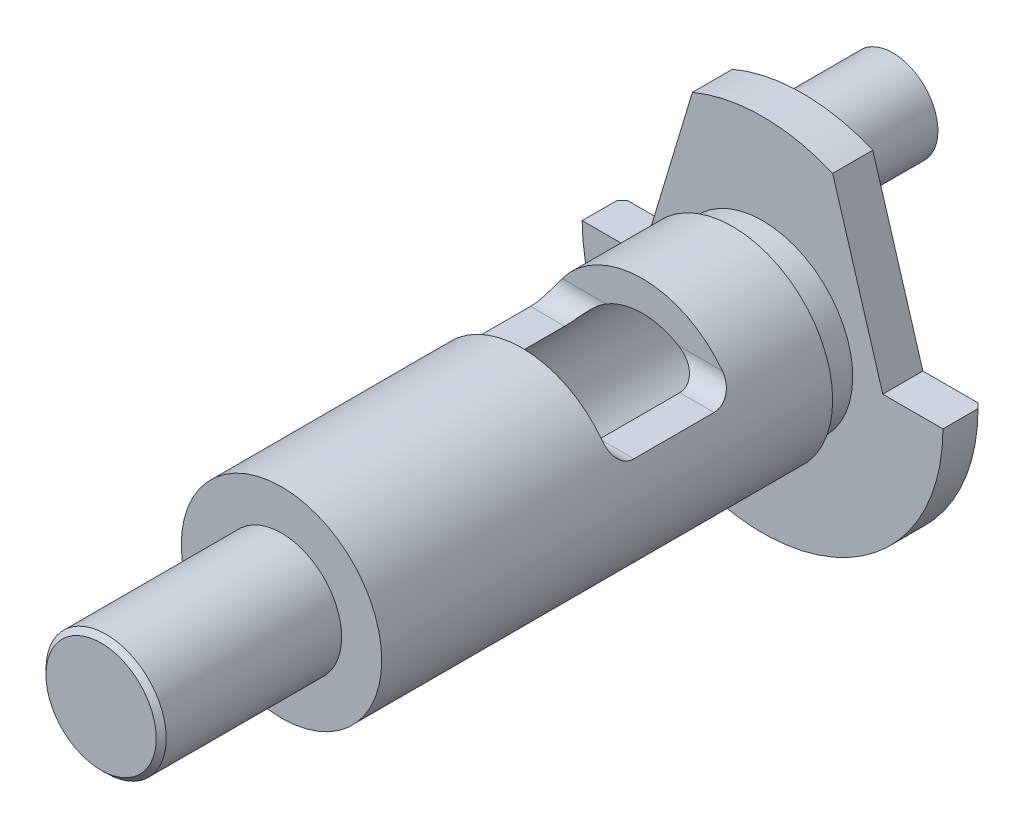
SolidWorks part; units mm, degrees
ref_plane "Plan de face" through (0, 0, 0) normal (0, 0, 1) x (1, 0, 0)
ref_plane "Plan de dessus" through (0, 0, 0) normal (0, 1, 0) x (1, 0, 0)
ref_plane "Plan de droite" through (0, 0, 0) normal (1, 0, 0) x (0, 0, -1)
sketch "Esquisse2" plane through (0, 0, 0) normal (1, 0, 0) x (0, 0, -1)
  line L0 (0, 0) -> (-36, 0) construction
  line L1 (-36, 0) -> (-70, 0)
  line L2 (-70, 0) -> (-70, 6)
  line L3 (-70, 6) -> (-52, 6)
  line L4 (-52, 6) -> (-52, 10)
  line L5 (-52, 10) -> (-7, 10)
  line L6 (-7, 10) -> (-7, 9)
  line L7 (-7, 9) -> (-4, 9)
  line L8 (-4, 9) -> (-4, 18)
  line L9 (-4, 18) -> (0, 18)
  line L10 (0, 18) -> (0, 7)
  line L11 (0, 7) -> (-32, 7)
  line L12 (-32, 7) -> (-36, 0)
  line L13 (0, 7) -> (0, 0) construction
  dimension "D1" = 70
  dimension "D2" = 36
  dimension "D3" = 4
  dimension "D4" = 7
  dimension "D5" = 18
  dimension "D6" = 4
  dimension "D7" = 3
  dimension "D8" = 1
  dimension "D9" = 10
  dimension "D10" = 18
  dimension "D11" = 6
revolve "Révolution2" add sketch "Esquisse2" angle 360 about L0
sketch "Esquisse3" plane through (0, 0, 0) normal (1, 0, 0) x (0, 0, -1)
  line L0 (-16, 10) -> (-28, 10)
  line L1 (-7, 10) -> (-52, 10) construction
  line L2 (-28, 10) -> (-28, 6)
  line L3 (-26, 4) -> (-18, 4)
  line L4 (-16, 6) -> (-16, 10)
  line L5 (-7, -10) -> (-7, 10) construction
  arc A0 (-18, 4) -> (-16, 6) centre (-18, 6) ccw
  arc A1 (-28, 6) -> (-26, 4) centre (-26, 6) ccw
  dimension "D4" = 2
  dimension "D1" = 6
  dimension "D2" = 12
  dimension "D3" = 9
extrude "Enlèv. mat.-Extru.1" cut sketch "Esquisse3" against normal through all both and the other way through all
sketch "Esquisse4" plane through (0, 0, 0) normal (0, 0, -1) x (-1, 0, 0)
  line L0 (-18, 0) -> (-12, 0)
  line L1 (-12, 0) -> (-7, 16.5831)
  line L2 (7, 16.5831) -> (12, 0)
  line L3 (12, 0) -> (18, 0)
  circle A0 centre (0, 0) radius 18 construction
  arc A1 (-7, 16.5831) -> (7, 16.5831) centre (0, 0) cw
  arc A2 (-18, 0) -> (18, 0) centre (0, 0) ccw
  dimension "D1" = 12
  dimension "D2" = 12
  dimension "D3" = 7
  dimension "D4" = 7
extrude "Enlèv. mat.-Extru.2" cut sketch "Esquisse4" against normal blind 10 flip side to cut
sketch "Esquisse5" plane through (0, 0, 0) normal (0, 0, -1) x (-1, 0, 0)
  line L0 (0, 0) -> (0, 18) construction
  arc A0 (7, 16.5831) -> (-7, 16.5831) centre (0, 0) ccw construction
  circle A1 centre (0, 12.5) radius 4.5
  dimension "D2" = 9
  dimension "D1" = 12.5
extrude "Boss.-Extru.1" add sketch "Esquisse5" along normal blind 9
chamfer "Chanfrein1" distance 0.5 3 edges at (0, 6, 70) (0, -18, 0) (0, 17, 0)
